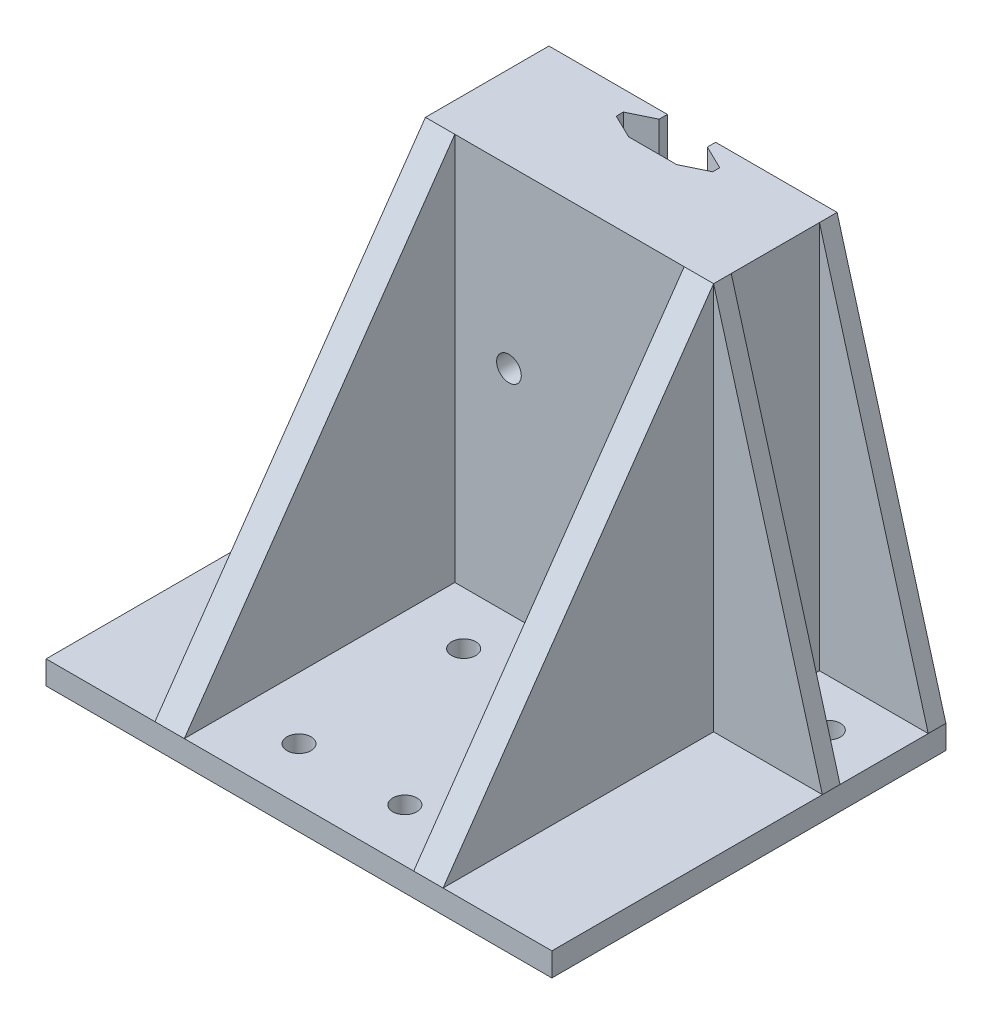
SolidWorks part; units mm, degrees
ref_plane "Спереди" through (0, 0, 0) normal (0, 0, 1) x (1, 0, 0)
ref_plane "Сверху" through (0, 0, 0) normal (0, 1, 0) x (1, 0, 0)
ref_plane "Справа" through (0, 0, 0) normal (1, 0, 0) x (0, 0, -1)
sketch "Эскиз1" plane through (0, 0, 0) normal (0, 0, 1) x (1, 0, 0)
  line L0 (-13.125, 2.6988) -> (-15.5, 2.6988)
  line L3 (6.875, 0.6988) -> (-7.075, 0.6988)
  line L6 (-13.125, 0.6988) -> (-13.125, 2.6988)
  line L16 (-7.075, 0.6988) -> (-7.075, 2.6988)
  line L17 (-15.5, 2.6988) -> (-15.5, 4.1388)
  line L18 (-15.5, 4.1388) -> (-12.84, 6.7988)
  line L19 (-12.84, 6.7988) -> (-7.36, 6.7988)
  line L20 (-7.36, 6.7988) -> (-4.7, 4.1388)
  line L21 (-4.7, 4.1388) -> (-4.7, 2.6988)
  line L22 (-4.7, 2.6988) -> (-7.075, 2.6988)
  line L35 (4.5, 2.6988) -> (6.875, 2.6988)
  line L41 (6.875, 0.6988) -> (6.875, 2.6988)
  line L42 (12.925, 0.6988) -> (12.925, 2.6988)
  line L66 (-24.35, 0.6988) -> (-13.125, 0.6988)
  line L68 (-24.35, 0.6988) -> (-24.35, -29.3012)
  line L69 (-24.35, -29.3012) -> (-19.45, -29.3012)
  line L70 (-19.45, -4.9012) -> (-19.45, -29.3012)
  line L73 (24.65, 0.6988) -> (24.65, -29.3012)
  line L74 (24.65, -29.3012) -> (15.25, -29.3012)
  line L75 (15.25, -4.9012) -> (15.25, -29.3012)
  line L77 (12.925, 0.6988) -> (24.65, 0.6988)
  line L78 (-19.45, -4.9012) -> (15.25, -4.9012)
  line L79 (4.5, 2.6988) -> (4.5, 4.1388)
  line L80 (4.5, 4.1388) -> (7.16, 6.7988)
  line L81 (7.16, 6.7988) -> (12.64, 6.7988)
  line L84 (12.64, 6.7988) -> (15.3, 4.1388)
  line L85 (15.3, 4.1388) -> (15.3, 2.6988)
  line L86 (15.3, 2.6988) -> (12.925, 2.6988)
  point P0 (0, 0)
  dimension "D2" = 9.4
  dimension "D3" = 1.44
  dimension "D4" = 2
  dimension "D5" = 49
  dimension "D6" = 4.1
  dimension "D7" = 5.48
  dimension "D8" = 2
  dimension "D9" = 6.05
  dimension "D10" = 30
  dimension "D11" = 10.8
  dimension "D12" = 2
  dimension "D13" = 1.44
  dimension "D14" = 2.66
  dimension "D15" = 24.4
  dimension "D16" = 30
  dimension "D17" = 5.6
  dimension "D18" = 4.9
  dimension "D19" = 2.325
  dimension "D20" = 1.44
  dimension "D21" = 2.66
  dimension "D22" = 5.48
  dimension "D23" = 8.85
  dimension "D24" = 10.8
  dimension "D25" = 1.44
  dimension "D26" = 2
  dimension "D27" = 6.05
  dimension "D29" = 2.375
  dimension "D30" = 2.375
  dimension "D31" = 2.375
  dimension "D32" = 4.1
extrude "Бобышка-Вытянуть1" add sketch "Эскиз1" along normal blind 17
sketch "Эскиз3" plane through (0, 0, 0) normal (0, 0, -1) x (-1, 0, 0)
  line L0 (24.35, -29.3012) -> (19.45, -29.3012) construction
  line L20 (19.25, -10.8012) -> (21.25, -10.8012)
  line L21 (19.25, -10.8012) -> (19.25, -23.3012)
  line L22 (19.25, -23.3012) -> (21.25, -23.3012)
  line L23 (21.25, -10.8012) -> (21.25, -23.3012)
  dimension "D1" = 6
  dimension "D4" = 12.5
  dimension "D5" = 2
sketch "Эскиз5" plane through (-24.35, 0, 0) normal (-1, 0, 0) x (0, 0, 1)
  line L0 (0, 0.6988) -> (0, -29.3012) construction
  line L2 (17, -29.3012) -> (0, -29.3012) construction
  circle A0 centre (9, -17.3012) radius 3
  dimension "D1" = 6
  dimension "D2" = 12
  dimension "D3" = 9
extrude "Вырез-Вытянуть3" cut sketch "Эскиз5" against normal up to surface (49 mm away) up to face at (24.65, -14.3012, 8.5)
sketch "Эскиз6" plane through (0, 0, 17) normal (0, 0, 1) x (1, 0, 0)
  line L1 (-24.35, -29.3012) -> (24.65, -29.3012)
  line L2 (-24.35, -29.3012) -> (-24.35, -25.3012)
  line L3 (-24.35, -25.3012) -> (24.65, -25.3012)
  line L4 (24.65, -29.3012) -> (24.65, -25.3012)
  dimension "D1" = 4
  dimension "D2" = 49
extrude "Бобышка-Вытянуть3" add sketch "Эскиз6" along normal blind 50
sketch "Эскиз7" plane through (-24.35, 0, 0) normal (-1, 0, 0) x (0, 0, 1)
  line L1 (0, -29.3012) -> (67, -29.3012)
  line L2 (0, -29.3012) -> (0, -25.3012)
  line L3 (0, -25.3012) -> (67, -25.3012)
  line L4 (67, -29.3012) -> (67, -25.3012)
extrude "Бобышка-Вытянуть4" add sketch "Эскиз7" along normal blind 18.5
sketch "Эскиз8" plane through (24.65, 0, 0) normal (1, 0, 0) x (0, 0, -1)
  line L1 (-67, -29.3012) -> (0, -29.3012)
  line L2 (-67, -29.3012) -> (-67, -25.3012)
  line L3 (-67, -25.3012) -> (0, -25.3012)
  line L4 (0, -29.3012) -> (0, -25.3012)
  dimension "D1" = 4
extrude "Бобышка-Вытянуть5" add sketch "Эскиз8" along normal blind 18.5
sketch "Эскиз14" plane through (0, -25.3012, 0) normal (0, 1, 0) x (1, 0, 0)
  line L0 (43.15, -17) -> (-42.85, -17) construction
  line L5 (-24.35, -17) -> (24.65, -17)
  line L6 (-24.35, -17) -> (-24.35, -21)
  line L7 (-24.35, -21) -> (24.65, -21)
  line L8 (24.65, -17) -> (24.65, -21)
  line L9 (-42.85, -67) -> (-42.85, 0) construction
  dimension "D1" = 4
  dimension "D2" = 49
  dimension "D3" = 18.5
extrude "Бобышка-Вытянуть13" add sketch "Эскиз14" along normal blind 66
sketch "Эскиз23" plane through (0, 0, 17) normal (0, 0, -1) x (-1, 0, 0)
  line L0 (24.35, 40.6988) -> (24.35, 0.6988) construction
  line L1 (-24.65, 40.6988) -> (24.35, 40.6988)
  line L2 (-24.65, 40.6988) -> (-24.65, 20.7988)
  line L3 (-24.65, 20.7988) -> (24.35, 20.7988)
  line L4 (24.35, 40.6988) -> (24.35, 20.7988)
  dimension "D1" = 19.9
extrude "Бобышка-Вытянуть18" add sketch "Эскиз23" along normal blind 17 contours L3 L4 L1 L2
sketch "Эскиз13" plane through (0, -25.3012, 0) normal (0, 1, 0) x (1, 0, 0)
  line L0 (43.15, -67) -> (-42.85, -67) construction
  line L1 (-42.85, -67) -> (-42.85, 0) construction
  line L2 (-42.85, -67) -> (-42.85, 0) construction
  line L3 (43.15, 0) -> (43.15, -67) construction
  line L4 (-42.85, 0) -> (-24.35, 0) construction
  line L5 (43.15, 0) -> (24.65, 0) construction
  circle A0 centre (-8.85, -58) radius 2.05
  circle A1 centre (9.15, -58) radius 2.05
  circle A2 centre (-33.85, -11) radius 2.05
  circle A3 centre (34.15, -11) radius 2.05
  circle A4 centre (-8.85, -30) radius 2.05
  circle A5 centre (9.15, -30) radius 2.05
  dimension "D1" = 4.1
  dimension "D2" = 4.1
  dimension "D3" = 4.1
  dimension "D4" = 4.1
  dimension "D8" = 4.1
  dimension "D13" = 4.1
  dimension "D5" = 9
  dimension "D6" = 9
  dimension "D7" = 18
  dimension "D9" = 9
  dimension "D10" = 9
  dimension "D11" = 11
  dimension "D12" = 11
  dimension "D14" = 28
  dimension "D15" = 28
  dimension "D16" = 34
  dimension "D17" = 34
  dimension "D18" = 18
extrude "Вырез-Вытянуть4" cut sketch "Эскиз13" against normal up to next
sketch "Эскиз16" plane through (-24.35, 0, 0) normal (-1, 0, 0) x (0, 0, 1)
  line L0 (21, -25.3012) -> (21, 40.6988)
  line L1 (21, 40.6988) -> (67, -25.3012)
  line L2 (67, -25.3012) -> (21, -25.3012)
extrude "Бобышка-Вытянуть14" add sketch "Эскиз16" against normal blind 5
sketch "Эскиз17" plane through (24.65, 0, 0) normal (1, 0, 0) x (0, 0, -1)
  line L0 (-67, -25.3012) -> (-21, 40.6988)
  line L1 (-21, 40.6988) -> (-21, -25.3012)
  line L2 (-21, -25.3012) -> (-67, -25.3012)
extrude "Бобышка-Вытянуть15" add sketch "Эскиз17" against normal blind 5
sketch "Эскиз18" plane through (0, 0, 21) normal (0, 0, 1) x (1, 0, 0)
  line L0 (-42.85, -29.3012) -> (43.15, -29.3012) construction
  line L1 (19.65, -25.3012) -> (19.65, 40.6988) construction
  circle A0 centre (9.85, 10.7988) radius 2.1
  circle A1 centre (-10.15, 10.7988) radius 2.1
  dimension "D1" = 4.2
  dimension "D2" = 4.2
  dimension "D3" = 20
  dimension "D4" = 40.1
  dimension "D5" = 9.8
  dimension "D6" = 40.1
extrude "Вырез-Вытянуть5" cut sketch "Эскиз18" against normal up to next
sketch "Эскиз21" plane through (0, 0, 0) normal (0, 0, -1) x (-1, 0, 0)
  line L1 (-15.25, -4.9012) -> (19.25, -4.9012)
  line L2 (-15.25, -4.9012) -> (-15.25, -4.2012)
  line L3 (-15.25, -4.2012) -> (19.25, -4.2012)
  line L4 (19.25, -4.9012) -> (19.25, -4.2012)
  dimension "D1" = 34.5
  dimension "D2" = 0.7
extrude "Вырез-Вытянуть6" cut sketch "Эскиз21" against normal blind 4.6
sketch "Эскиз25" plane through (0, 0, 0) normal (0, 0, -1) x (-1, 0, 0)
  line L0 (-24.65, 40.6988) -> (-24.65, -25.3012)
  line L1 (-24.65, -25.3012) -> (-43.15, -25.3012)
  line L2 (-43.15, -25.3012) -> (-24.65, 40.6988)
  line L3 (42.85, -25.3012) -> (24.35, -25.3012)
  line L4 (24.35, -25.3012) -> (24.35, 40.6988)
  line L5 (24.35, 40.6988) -> (42.85, -25.3012)
extrude "Бобышка-Вытянуть19" add sketch "Эскиз25" against normal blind 3
sketch "Эскиз28" plane through (0, 0, 21) normal (0, 0, 1) x (1, 0, 0)
  line L0 (43.15, -25.3012) -> (24.65, -25.3012)
  line L1 (24.65, -25.3012) -> (24.65, 40.6988)
  line L2 (24.65, 40.6988) -> (43.15, -25.3012)
  line L3 (-24.35, -25.3012) -> (-42.85, -25.3012)
  line L4 (-42.85, -25.3012) -> (-24.35, 40.6988)
  line L5 (-24.35, 40.6988) -> (-24.35, -25.3012)
extrude "Бобышка-Вытянуть20" add sketch "Эскиз28" against normal blind 3
sketch "Эскиз29" plane through (0, 0.6988, 0) normal (0, 1, 0) x (1, 0, 0)
  line L0 (-13.125, -17) -> (-24.35, -17) construction
  line L1 (-24.35, 0) -> (-20.2, 0)
  line L2 (-24.35, 0) -> (-24.35, -17)
  line L3 (-24.35, -17) -> (-20.2, -17)
  line L4 (-20.2, 0) -> (-20.2, -17)
  line L5 (20, -17) -> (24.65, -17)
  line L6 (24.65, 0) -> (20, 0)
  line L7 (24.65, 0) -> (24.65, -17)
  line L9 (20, 0) -> (20, -17)
  dimension "D1" = 4.15
  dimension "D2" = 4.65
extrude "Бобышка-Вытянуть21" add sketch "Эскиз29" along normal up to next
extrude "Вырез-Вытянуть7" cut sketch "Эскиз3" against normal up to surface (17 mm away) up to face at (-2.1, -17.1012, 17)
sketch "Эскиз30" plane through (0, 40.6988, 0) normal (0, 1, 0) x (1, 0, 0)
  line L0 (24.65, 0) -> (-24.35, 0) construction
  line L1 (-4.2, 0) -> (4, 0)
  line L2 (-4.2, 0) -> (-4.2, -1.4)
  line L4 (4, 0) -> (4, -1.4)
  line L5 (-24.35, 0) -> (-24.35, -3) construction
  line L11 (-4.2, -1.4) -> (-8.3, -3.4)
  line L12 (4, -1.4) -> (8.1, -3.4)
  line L13 (-8.3, -3.4) -> (-8.3, -4.6)
  line L14 (-8.3, -4.6) -> (-4.2, -6.6)
  line L15 (-4.2, -6.6) -> (4, -6.6)
  line L16 (4, -6.6) -> (8.1, -4.6)
  line L17 (8.1, -4.6) -> (8.1, -3.4)
  dimension "D1" = 8.2
  dimension "D2" = 1.4
  dimension "D3" = 20.15
  dimension "D4" = 1.2
  dimension "D5" = 6.6
  dimension "D6" = 1.2
  dimension "D7" = 3.4
  dimension "D8" = 3.4
  dimension "D9" = 4.1
  dimension "D10" = 4.2
  dimension "D11" = 1.4
  dimension "D12" = 4.1
extrude "Вырез-Вытянуть8" cut sketch "Эскиз30" against normal blind 20
